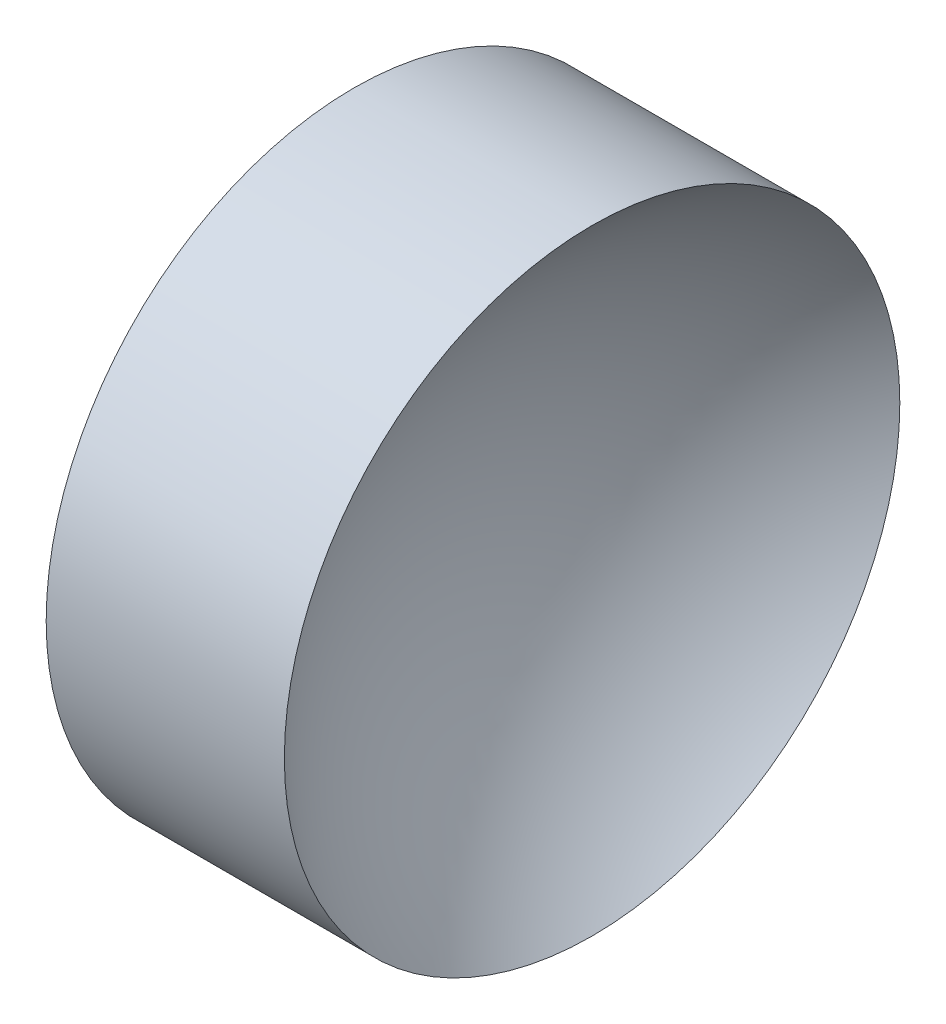
SolidWorks part; units mm, degrees
ref_plane "前视基准面" through (0, 0, 0) normal (0, 0, 1) x (1, 0, 0)
ref_plane "上视基准面" through (0, 0, 0) normal (0, 1, 0) x (1, 0, 0)
ref_plane "右视基准面" through (0, 0, 0) normal (1, 0, 0) x (0, 0, -1)
sketch "草图1" plane through (0, 0, 0) normal (0, 0, 1) x (1, 0, 0)
  line L0 (42.4499, 26.089) -> (53.384, 26.089) construction
  line L1 (44.3196, 26.089) -> (44.3196, 31.089)
  line L2 (45.8196, 26.089) -> (44.3196, 26.089)
  line L3 (44.3196, 31.089) -> (48.1896, 31.089)
  arc A0 (48.1896, 31.089) -> (45.8196, 26.089) centre (52.2788, 26.089) ccw
revolve "旋转1" add sketch "草图1" angle 360 about L0
